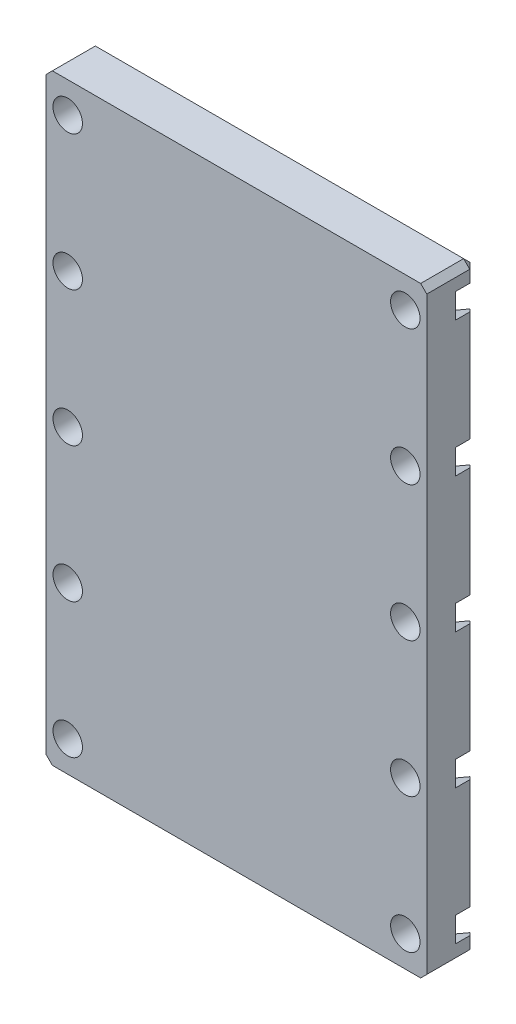
SolidWorks part; units mm, degrees
material "ABS"
ref_plane "正面" through (0, 0, 0) normal (0, 0, 1) x (1, 0, 0)
ref_plane "平面" through (0, 0, 0) normal (0, 1, 0) x (1, 0, 0)
ref_plane "右側面" through (0, 0, 0) normal (1, 0, 0) x (0, 0, -1)
sketch "ｽｹｯﾁ1" plane through (0, 0, 0) normal (0, 0, 1) x (1, 0, 0)
  line L1 (-31, 49) -> (31, 49)
  line L2 (-31, 49) -> (-31, -49)
  line L3 (-31, -49) -> (31, -49)
  line L4 (31, 49) -> (31, -49)
  line L5 (-31, 49) -> (31, -49) construction
  line L6 (-31, -49) -> (31, 49) construction
  point P0 (0, 0)
  dimension "D1" = 98
  dimension "D2" = 62
extrude "ﾎﾞｽ - 押し出し1" add sketch "ｽｹｯﾁ1" along normal blind 8
sketch "ｽｹｯﾁ2" plane through (0, 0, 8) normal (0, 0, 1) x (1, 0, 0)
  line L0 (0, 49) -> (0, -49) construction
  line L1 (31, 49) -> (-31, 49) construction
  line L2 (-31, -49) -> (31, -49) construction
  line L3 (-27.5, 49) -> (-27.5, -49) construction
  line L4 (-31, 0) -> (31, 0) construction
  line L5 (-31, 49) -> (-31, -49) construction
  line L6 (31, -49) -> (31, 49) construction
  dimension "D1" = 27.5
chamfer "面取り1" distance 1 angle 45 8 edges at (0, 49, 0) (31, 49, 4) (31, 0, 0) (31, -49, 4) (0, -49, 0) (-31, -49, 4) (-31, 0, 0) (-31, 49, 4)
hole_wizard "M4 すきま穴1" positions "ｽｹｯﾁ4" profile "ｽｹｯﾁ5" hole size "M4" standard "JIS" end condition through all
sketch "ｽｹｯﾁ4" plane through (0, 0, 8) normal (0, 0, 1) x (1, 0, 0)
  line L0 (-27.5, 49) -> (-27.5, -49) construction
  line L1 (30, 49) -> (-30, 49) construction
  line L2 (-31, 22) -> (31, 22) construction
  line L3 (-31, 48) -> (-31, -48) construction
  line L4 (31, -48) -> (31, 48) construction
  point P0 (-27.5, 44)
  point P7 (-27.5, 22)
  point P9 (-27.5, 0)
  dimension "D1" = 5
sketch "ｽｹｯﾁ5" plane through (-27.5, 44, 8) normal (1, 0, 0) x (0, -1, 0)
  line L0 (0, 0) -> (0, 8)
  line L1 (0, 8) -> (2.4, 8)
  line L2 (2.4, 8) -> (2.4, 0)
  line L5 (2.4, 0) -> (0, 0)
  line L11 (0, -6.35) -> (0, 107.95) construction
  dimension "通し穴の直径" = 4.8
  dimension "通し穴の深さ" = 8
sketch "ｽｹｯﾁ6" plane through (0, 0, 0) normal (0, 0, -1) x (-1, 0, 0)
  line L0 (27.5, 17.9585) -> (31, 19.9793)
  line L1 (27.5, 39.9585) -> (31, 41.9793)
  line L2 (31, 41.9793) -> (31, 46.0207)
  line L3 (31, 46.0207) -> (27.5, 48.0415)
  line L4 (27.5, 48.0415) -> (24, 46.0207)
  line L5 (24, 46.0207) -> (24, 41.9793)
  line L6 (24, 41.9793) -> (27.5, 39.9585)
  line L7 (31, 19.9793) -> (31, 24.0207)
  line L8 (31, 24.0207) -> (27.5, 26.0415)
  line L9 (27.5, 26.0415) -> (24, 24.0207)
  line L10 (24, 24.0207) -> (24, 19.9793)
  line L11 (24, 19.9793) -> (27.5, 17.9585)
  line L12 (27.5, -4.0415) -> (31, -2.0207)
  line L13 (31, -2.0207) -> (31, 2.0207)
  line L14 (31, 2.0207) -> (27.5, 4.0415)
  line L15 (27.5, 4.0415) -> (24, 2.0207)
  line L16 (24, 2.0207) -> (24, -2.0207)
  line L17 (24, -2.0207) -> (27.5, -4.0415)
  circle A0 centre (27.5, 44) radius 3.5 construction
  circle A1 centre (27.5, 22) radius 3.5 construction
  circle A2 centre (27.5, 0) radius 3.5 construction
  circle A3 centre (27.5, 22) radius 2.4 construction
  dimension "D1" = 7
  dimension "D2" = 3
extrude "ｶｯﾄ - 押し出し1" cut sketch "ｽｹｯﾁ6" against normal blind 3.3
mirror "ﾐﾗｰ1" about plane through (0, 0, 0) normal (0, 1, 0) of "M4 すきま穴1", "ｶｯﾄ - 押し出し1"
mirror "ﾐﾗｰ2" about plane through (0, 0, 0) normal (1, 0, 0) of "ﾐﾗｰ1", "M4 すきま穴1", "ｶｯﾄ - 押し出し1"
